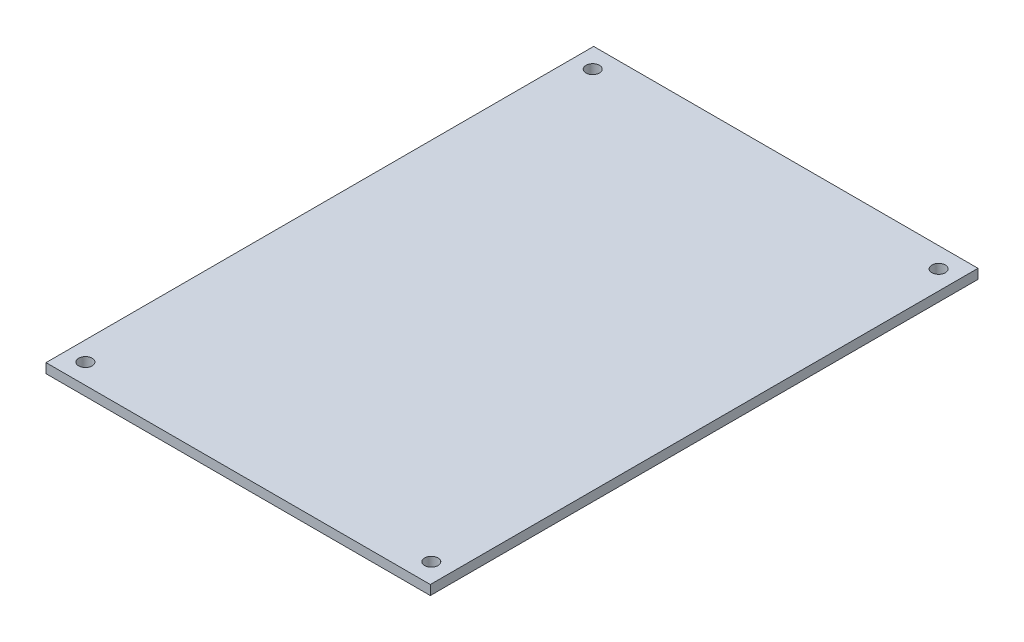
SolidWorks part; units mm, degrees
ref_plane "Front Plane" through (0, 0, 0) normal (0, 0, 1) x (1, 0, 0)
ref_plane "Top Plane" through (0, 0, 0) normal (0, 1, 0) x (1, 0, 0)
ref_plane "Right Plane" through (0, 0, 0) normal (1, 0, 0) x (0, 0, -1)
sketch "Sketch1" plane through (0, 0, 0) normal (0, 1, 0) x (1, 0, 0)
  line L1 (50.8, 72.39) -> (-50.8, 72.39)
  line L2 (50.8, 72.39) -> (50.8, -72.39)
  line L3 (50.8, -72.39) -> (-50.8, -72.39)
  line L4 (-50.8, 72.39) -> (-50.8, -72.39)
  line L5 (50.8, 72.39) -> (-50.8, -72.39) construction
  line L6 (50.8, -72.39) -> (-50.8, 72.39) construction
  point P0 (0, 0)
  dimension "D1" = 144.78
  dimension "D2" = 101.6
extrude "Boss-Extrude1" add sketch "Sketch1" along normal blind 2.54
sketch "Sketch2" plane through (0, 2.54, 0) normal (0, 1, 0) x (1, 0, 0)
  line L2 (50.8, 72.39) -> (-50.8, 72.39) construction
  line L3 (-50.8, 72.39) -> (-50.8, -72.39) construction
  circle A0 centre (-45.72, 67.056) radius 1.778
  circle A1 centre (-45.72, -67.056) radius 1.778
  circle A2 centre (45.72, -67.056) radius 1.778
  circle A3 centre (45.72, 67.056) radius 1.778
  point P12 (-52.8441, 56.9692)
  dimension "D1" = 3.556
  dimension "D2" = 91.44
  dimension "D3" = 134.112
  dimension "D4" = 5.334
  dimension "D5" = 5.08
extrude "Cut-Extrude1" cut sketch "Sketch2" against normal blind 2.54
